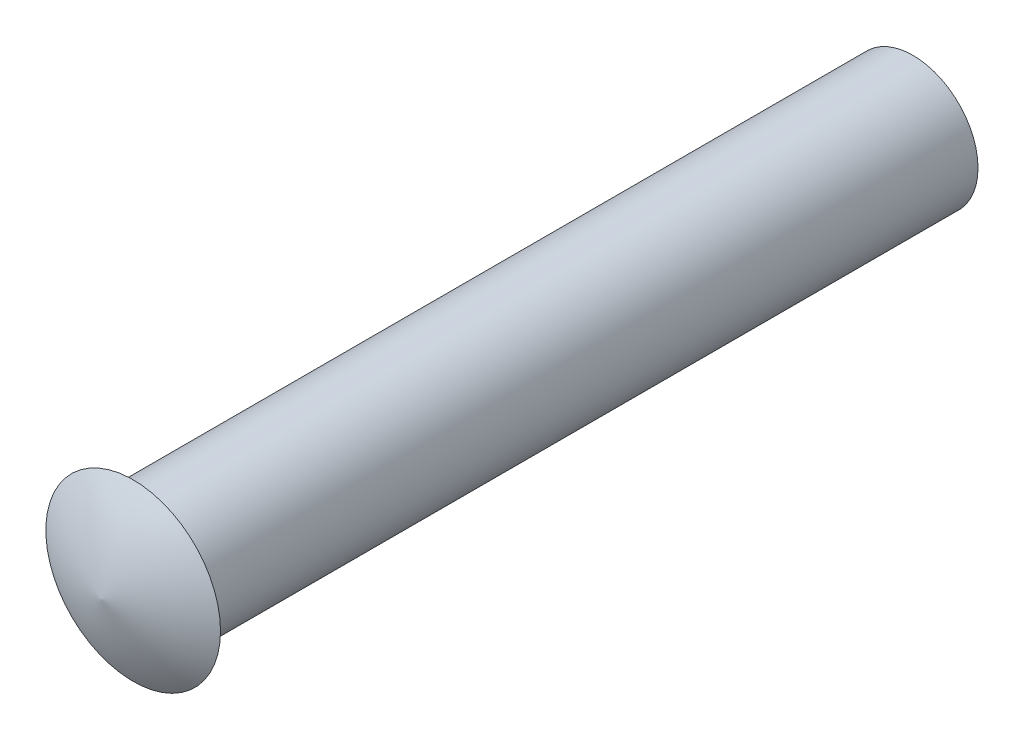
SolidWorks part; units mm, degrees
ref_plane "Front Plane" through (0, 0, 0) normal (0, 0, 1) x (1, 0, 0)
ref_plane "Top Plane" through (0, 0, 0) normal (0, 1, 0) x (1, 0, 0)
ref_plane "Right Plane" through (0, 0, 0) normal (1, 0, 0) x (0, 0, -1)
sketch "Sketch1" plane through (0, 0, 0) normal (1, 0, 0) x (0, 0, -1)
  line L0 (0, 0) -> (19.8374, 0)
  line L1 (0.7874, 2.1336) -> (0.7874, 1.5875)
  line L2 (19.8374, 1.5875) -> (19.8374, 0)
  line L3 (0.7874, 1.5875) -> (19.8374, 1.5875)
  arc A0 (0, 0) -> (0.7874, 2.1336) centre (5.6742, -0.8819) cw
  point P7 (0.7874, 1.8606)
  dimension "D1" = 1.5875
  dimension "D2" = 19.05
  dimension "D3" = 0.7874
  dimension "D4" = 2.1336
revolve "Revolve1" add sketch "Sketch1" angle 360 about L0
